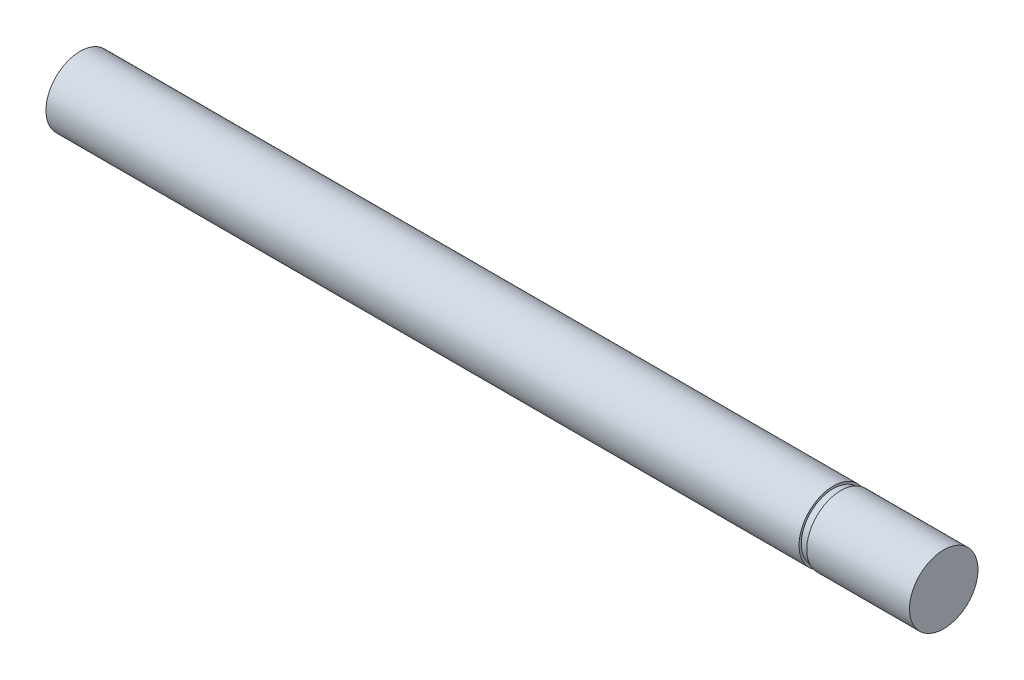
SolidWorks part; units mm, degrees
ref_plane "Front Plane" through (0, 0, 0) normal (0, 0, 1) x (1, 0, 0)
ref_plane "Top Plane" through (0, 0, 0) normal (0, 1, 0) x (1, 0, 0)
ref_plane "Right Plane" through (0, 0, 0) normal (1, 0, 0) x (0, 0, -1)
sketch "Sketch1" plane through (0, 0, 0) normal (1, 0, 0) x (0, 0, -1)
  circle A0 centre (0, 0) radius 6.35
  dimension "D1" = 12.7
extrude "Boss-Extrude1" add sketch "Sketch1" along normal mid plane 139.5984
sketch "Sketch2" plane through (0, 0, 0) normal (0, 0, 1) x (1, 0, 0)
  line L0 (69.7992, -6.35) -> (69.7992, 6.35) construction
  line L1 (71.2216, 5.9436) -> (69.7992, 5.9436)
  line L5 (0, 0) -> (98.3976, 0) construction
  line L7 (69.7992, 5.9436) -> (69.7992, 0)
  line L9 (69.7992, 0) -> (71.2216, 0)
  line L10 (71.2216, 0) -> (71.2216, 5.9436)
  dimension "D1" = 1.4224
  dimension "D2" = 11.8872
revolve "Revolve2" add sketch "Sketch2" angle 360 about L5
sketch "Sketch3" plane through (71.2216, 0, 0) normal (1, 0, 0) x (0, 0, -1)
  circle A1 centre (0, 0) radius 6.35
  circle A2 centre (0, 0) radius 6.35
  dimension "D1" = 0
extrude "Boss-Extrude2" add sketch "Sketch3" along normal blind 19.05
hole_wizard "1/4-20 Tapped Hole1" positions "Sketch8" profile "Sketch10" tap size "1/4-20" standard "ANSI Inch"
sketch "Sketch8" plane through (-69.7992, 0, 0) normal (-1, 0, 0) x (0, 0, 1)
  point P0 (0, 0)
sketch "Sketch10" plane through (-69.7992, 0, 0) normal (0, 1, 0) x (0, 0, 1)
  line L0 (0, 0) -> (0, 18.0438)
  line L1 (0, 18.0438) -> (2.5527, 16.51)
  line L2 (2.5527, 16.51) -> (2.5527, 0)
  line L5 (2.5527, 0) -> (0, 0)
  line L10 (0, 18.0438) -> (-2.5527, 16.51) construction
  line L11 (0, -6.35) -> (0, 107.95) construction
  dimension "Tap Drill Dia." = 5.1054
  dimension "Tap Drill Depth" = 16.51
  dimension "Drill Angle" = 118
equation "\"ShaftDia\"=0.5"
equation "\"D1\"= \"YokeWidth\""
equation "\"EncoderWidth\"=0.75"
equation "\"D1@Boss-Extrude2\"=\"EncoderWidth\""
